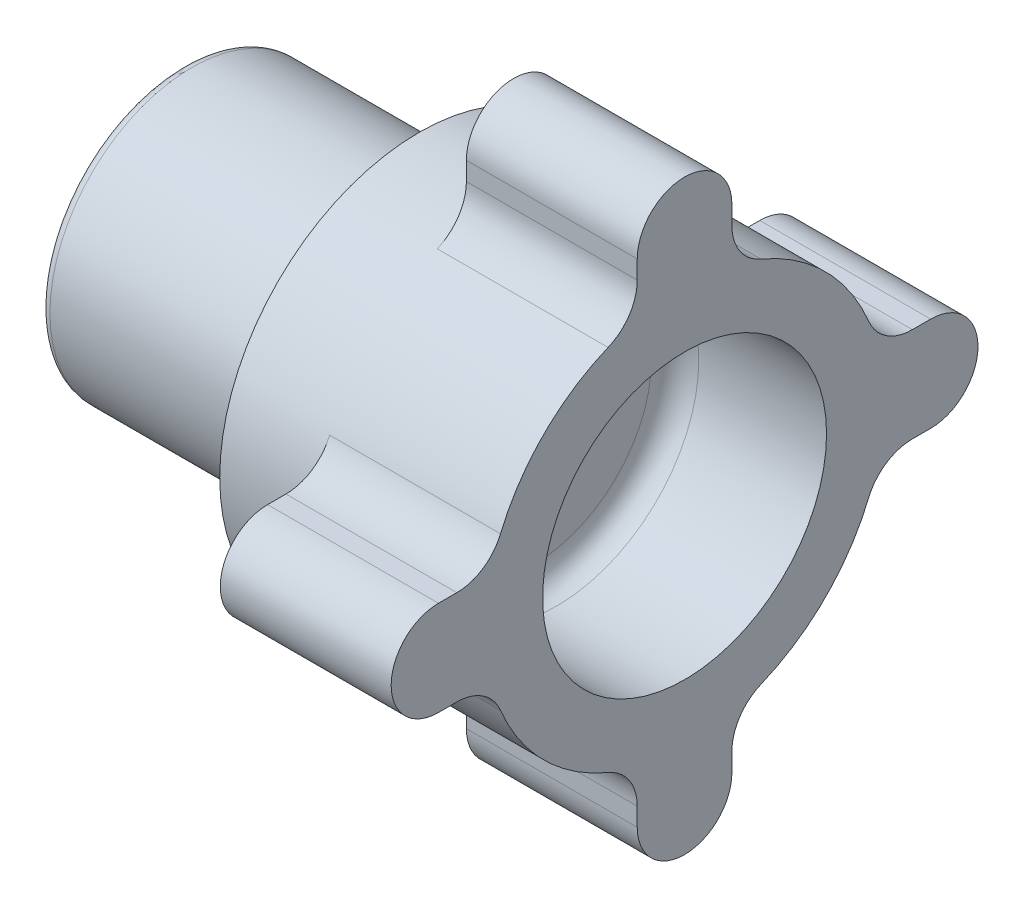
SolidWorks part; units mm, degrees
material "Plain Carbon Steel"
ref_plane "Front" through (0, 0, 0) normal (0, 0, 1) x (1, 0, 0)
ref_plane "Top" through (0, 0, 0) normal (0, 1, 0) x (1, 0, 0)
ref_plane "Right" through (0, 0, 0) normal (1, 0, 0) x (0, 0, -1)
sketch "Sketch1" plane through (0, 0, 0) normal (0, 0, 1) x (1, 0, 0)
  line L0 (479.9414, 251.46) -> (511.6914, 251.46)
  line L1 (524.3914, 259.155) -> (524.3914, 271.78)
  line L2 (511.6914, 251.46) -> (511.6914, 259.155)
  line L3 (511.6914, 259.155) -> (524.3914, 259.155)
  line L4 (470.4164, 259.155) -> (470.4164, 205.665) construction
  line L5 (524.3914, 271.78) -> (547.3164, 271.78)
  line L6 (479.9414, 251.46) -> (479.9414, 238.76)
  line L7 (439.5414, 232.41) -> (559.3164, 232.41) construction
  line L8 (547.3164, 271.78) -> (547.3164, 238.76)
  line L12 (547.3164, 238.76) -> (479.9414, 238.76)
  line L14 (511.6914, 205.665) -> (511.6914, 259.155) construction
  line L15 (511.6914, 205.665) -> (511.6914, 259.155) construction
  point P7 (0, 0)
  dimension "D1" = 22.925
  dimension "D2" = 6.35
  dimension "D4" = 39.37
  dimension "D5" = 19.05
  dimension "D6" = 12.7
  dimension "D7" = 9.525
  dimension "D9" = 12.7
revolve "Revolve1" add sketch "Sketch1" angle 360 about L7
sketch "Sketch3" plane through (479.9414, 0, 0) normal (-1, 0, 0) x (0, 0, 1)
  circle A0 centre (0, 245.11) radius 3.175
  circle A1 centre (10.9985, 238.76) radius 3.175
  circle A2 centre (10.9985, 226.06) radius 3.175
  circle A3 centre (0, 219.71) radius 3.175
  circle A4 centre (-10.9985, 226.06) radius 3.175
  circle A5 centre (-10.9985, 238.76) radius 3.175
  circle A6 centre (0, 232.41) radius 6.35 construction
  point P4 (0, 232.41)
  point P14 (0, 232.41)
  dimension "D1" = 6.35
  dimension "D2" = 12.7
  dimension "D3" = 6
hole_wizard "3/16 (0.1875) Dowel Hole1" positions "3DSketch1" profile "Sketch4" hole size "3/16" standard "ANSI Inch"
sketch3d "3DSketch1"
  point P0 (479.9414, 238.76, -10.9985)
  point P3 (479.9414, 245.11, 0)
  point P6 (479.9414, 238.76, 10.9985)
  point P9 (479.9414, 226.06, 10.9985)
  point P12 (479.9414, 219.71, 0)
  point P15 (479.9414, 226.06, -10.9985)
sketch "Sketch4" plane through (479.9414, 238.76, -10.9985) normal (0, 1, 0) x (0, 0, 1)
  line L0 (0, 0) -> (0, 14.1308)
  line L1 (0, 14.1308) -> (2.3812, 12.7)
  line L2 (2.3812, 12.7) -> (2.3812, 0)
  line L5 (2.3812, 0) -> (0, 0)
  line L10 (0, 14.1308) -> (-2.3812, 12.7) construction
  line L11 (0, -6.35) -> (0, 107.95) construction
  dimension "Hole Dia." = 4.7625
  dimension "Hole Depth" = 12.7
  dimension "Drill Angle" = 118
sketch "Sketch5" plane through (524.3914, 0, 0) normal (-1, 0, 0) x (0, 0, 1)
  line L0 (-6.35, 265.43) -> (-6.35, 258.3903)
  line L1 (6.35, 265.43) -> (6.35, 258.3903)
  line L2 (33.02, 238.76) -> (25.9803, 238.76)
  line L3 (33.02, 226.06) -> (25.9803, 226.06)
  line L4 (6.35, 199.39) -> (6.35, 206.4297)
  line L5 (-6.35, 199.39) -> (-6.35, 206.4297)
  line L6 (-33.02, 226.06) -> (-25.9803, 226.06)
  line L7 (-33.02, 238.76) -> (-25.9803, 238.76)
  arc A1 (6.35, 265.43) -> (-6.35, 265.43) centre (0, 265.43) ccw
  circle A3 centre (0, 232.41) radius 26.745 construction
  circle A4 centre (0, 232.41) radius 26.745
  arc A5 (33.02, 226.06) -> (33.02, 238.76) centre (33.02, 232.41) ccw
  arc A7 (-6.35, 199.39) -> (6.35, 199.39) centre (0, 199.39) ccw
  arc A9 (-33.02, 238.76) -> (-33.02, 226.06) centre (-33.02, 232.41) ccw
  circle A11 centre (0, 232.41) radius 39.37 construction
  point P7 (0, 232.41)
  point P38 (0, 232.41)
  circle M4 centre (0, 232.41) radius 39.37
  circle M12 centre (0, 232.41) radius 26.745
  dimension "D1" = 12.7
  dimension "D2" = 4
extrude "Cut-Extrude3" cut sketch "Sketch5" against normal up to surface (22.925 mm away) contours A9 A7 L5 L6 M4 M12 | A9 L7 L0 A1 M12 M4 | A5 A1 L1 L2 M4 M12 | A7 A5 L3 L4 M4 M12 up to face at (547.3164, 232.41, 6.35)
sketch "Sketch6" plane through (547.3164, 0, 0) normal (1, 0, 0) x (0, 0, -1)
  circle A0 centre (0, 232.41) radius 19.05
  dimension "D1" = 38.1
extrude "Cut-Extrude4" cut sketch "Sketch6" against normal blind 20.32
fillet "Fillet8" radius 6.35 8 edges at (535.8539, 226.06, 25.9803) (535.8539, 206.4297, 6.35) (535.8539, 206.4297, -6.35) (535.8539, 226.06, -25.9803) (535.8539, 238.76, -25.9803) (535.8539, 258.3903, -6.35) (535.8539, 258.3903, 6.35) (535.8539, 238.76, 25.9803)
fillet "Fillet7" radius 1.27 2 edges at (479.9414, 232.41, 6.35) (479.9414, 232.41, 19.05)
fillet "Fillet9" radius 3.175 1 edges at (526.9964, 232.41, -19.05)
hole_wizard "1/4-20 Tapped Hole1" positions "3DSketch2" profile "Sketch7" tap size "1/4-20" standard "ANSI Inch"
sketch3d "3DSketch2"
  circle A4 centre (524.3914, 232.41, 0) radius 34.29
  circle A5 centre (481.2114, 232.41, 0) radius 6.35 construction
  point P0 (524.3914, 232.41, -34.29)
  point P2 (524.3914, 266.7, 0)
  point P4 (524.3914, 232.41, 34.29)
  point P6 (524.3914, 198.12, 0)
  point P33 (558.6814, 232.41, 0)
  point P38 (474.8614, 232.41, 0)
  dimension "D1" = 34.29
cosmetic thread "Hole Thread1" parameters "D1"=12.7, "D2"=6.35
cosmetic thread "Hole Thread2" parameters "D1"=12.7, "D2"=6.35
cosmetic thread "Hole Thread3" parameters "D1"=12.7, "D2"=6.35
cosmetic thread "Hole Thread4" parameters "D1"=12.7, "D2"=6.35
sketch "Sketch7" plane through (524.3914, 232.41, -34.29) normal (0, 1, 0) x (0, 0, 1)
  line L0 (0, 0) -> (0, 18.0438)
  line L1 (0, 18.0438) -> (2.5527, 16.51)
  line L2 (2.5527, 16.51) -> (2.5527, 0)
  line L5 (2.5527, 0) -> (0, 0)
  line L10 (0, 18.0438) -> (-2.5527, 16.51) construction
  line L11 (0, -6.35) -> (0, 107.95) construction
  dimension "Tap Drill Dia." = 5.1054
  dimension "Tap Drill Depth" = 16.51
  dimension "Drill Angle" = 118
